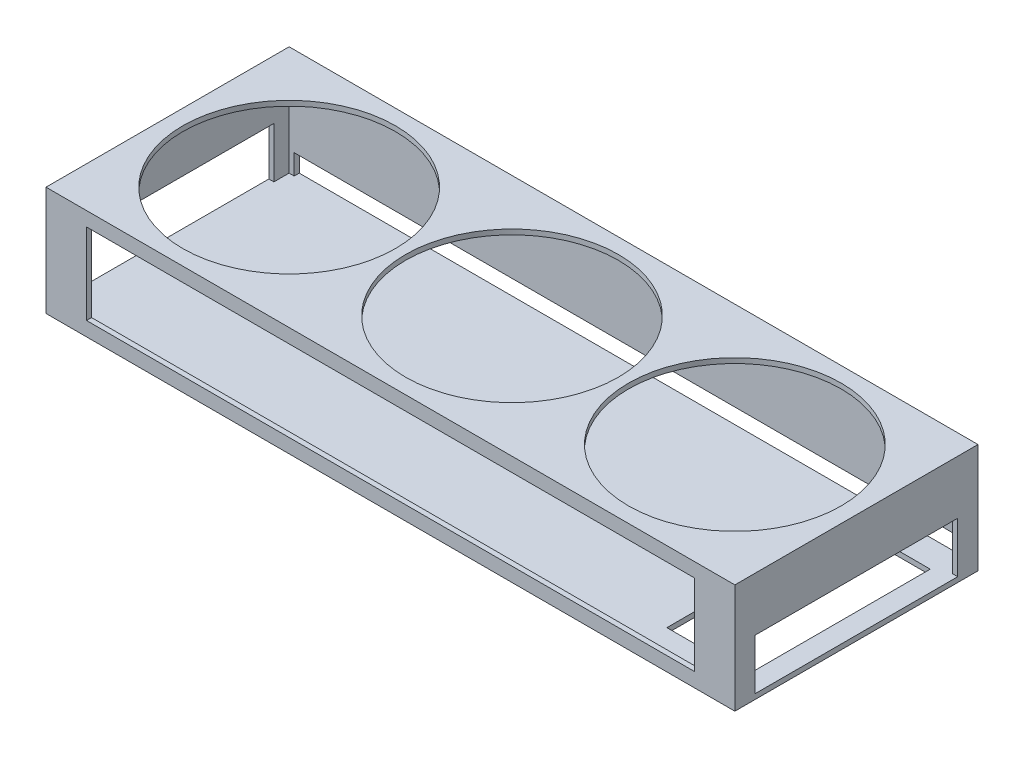
SolidWorks part; units mm, degrees
ref_plane "Front Plane" through (0, 0, 0) normal (0, 0, 1) x (1, 0, 0)
ref_plane "Top Plane" through (0, 0, 0) normal (0, 1, 0) x (1, 0, 0)
ref_plane "Right Plane" through (0, 0, 0) normal (1, 0, 0) x (0, 0, -1)
sketch "Sketch1" plane through (0, 0, 0) normal (0, 0, 1) x (1, 0, 0)
  line L1 (-170, -27) -> (170, -27)
  line L2 (-170, -27) -> (-170, 27)
  line L3 (-170, 27) -> (170, 27)
  line L4 (170, -27) -> (170, 27)
  line L5 (-170, -27) -> (170, 27) construction
  line L6 (-170, 27) -> (170, -27) construction
  point P0 (0, 0)
  dimension "D1" = 340
  dimension "D2" = 54
extrude "Boss-Extrude1" add sketch "Sketch1" along normal blind 120
shell "Shell1" thickness 2.5
sketch "Sketch2" plane through (0, 27, 0) normal (0, 1, 0) x (1, 0, 0)
  line L0 (-170, -120) -> (-170, 0) construction
  line L1 (170, -120) -> (170, 0) construction
  circle A0 centre (-110, -60) radius 52.5
  circle A1 centre (0, -60) radius 52.5
  circle A2 centre (110, -60) radius 52.5
  dimension "D1" = 105
  dimension "D2" = 60
  dimension "D3" = 60
extrude "Cut-Extrude1" cut sketch "Sketch2" against normal blind 10
sketch "Sketch3" plane through (0, 0, 120) normal (0, 0, 1) x (1, 0, 0)
  line L1 (-150, -20) -> (150, -20)
  line L2 (-150, -20) -> (-150, 20)
  line L3 (-150, 20) -> (150, 20)
  line L4 (150, -20) -> (150, 20)
  line L5 (-150, -20) -> (150, 20) construction
  line L6 (-150, 20) -> (150, -20) construction
  point P0 (0, 0)
  dimension "D1" = 300
  dimension "D2" = 40
extrude "Cut-Extrude2" cut sketch "Sketch3" against normal blind 10
sketch "Sketch4" plane through (170, 0, 0) normal (1, 0, 0) x (0, 0, -1)
  line L0 (-120, -27) -> (0, -27) construction
  line L1 (-110, 0.5) -> (-10, 0.5)
  line L2 (-110, 0.5) -> (-110, -24.5)
  line L3 (-110, -24.5) -> (-10, -24.5)
  line L4 (-10, 0.5) -> (-10, -24.5)
  line L5 (-110, 0.5) -> (-10, -24.5) construction
  line L6 (-110, -24.5) -> (-10, 0.5) construction
  point P0 (-60, -12)
  point P5 (0, 0)
  point P8 (-60, -27)
  dimension "D1" = 100
  dimension "D2" = 25
  dimension "D3" = 2.5
extrude "Cut-Extrude3" cut sketch "Sketch4" against normal through all
sketch "Sketch5" plane through (0, -27, 0) normal (0, -1, 0) x (1, 0, 0)
  line L0 (170, 120) -> (170, 0) construction
  line L1 (120, 13.5566) -> (160, 13.5566)
  line L2 (120, 13.5566) -> (120, 103.5566)
  line L3 (120, 103.5566) -> (160, 103.5566)
  line L4 (160, 13.5566) -> (160, 103.5566)
  line L5 (120, 13.5566) -> (160, 103.5566) construction
  line L6 (120, 103.5566) -> (160, 13.5566) construction
  point P0 (140, 58.5566)
  dimension "D1" = 40
  dimension "D2" = 10
  dimension "D3" = 90
extrude "Cut-Extrude4" cut sketch "Sketch5" against normal blind 10
sketch "Sketch6" plane through (0, 0, 0) normal (0, 0, -1) x (-1, 0, 0)
  line L0 (170, -27) -> (-170, -27) construction
  line L1 (165, -24.5) -> (-165, -24.5)
  line L2 (165, -24.5) -> (165, -14.5)
  line L3 (165, -14.5) -> (-165, -14.5)
  line L4 (-165, -24.5) -> (-165, -14.5)
  line L5 (165, -24.5) -> (-165, -14.5) construction
  line L6 (165, -14.5) -> (-165, -24.5) construction
  point P0 (0, -19.5)
  point P7 (0, 0)
  dimension "D1" = 2.5
  dimension "D2" = 10
  dimension "D3" = 330
extrude "Cut-Extrude5" cut sketch "Sketch6" against normal blind 10
